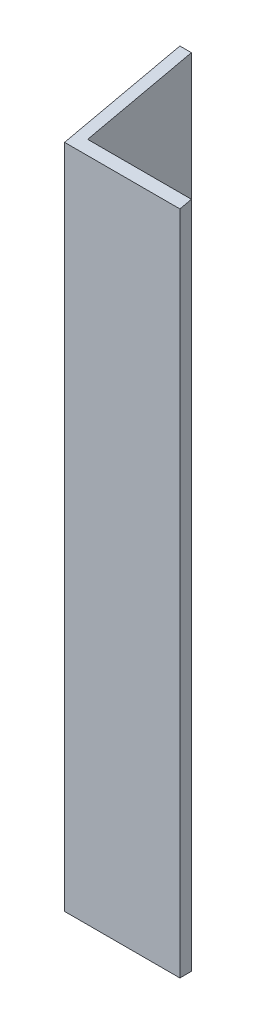
SolidWorks part; units mm, degrees
material "AISI 1020"
ref_plane "Front Plane" through (0, 0, 0) normal (0, 0, 1) x (1, 0, 0)
ref_plane "Top Plane" through (0, 0, 0) normal (0, 1, 0) x (1, 0, 0)
ref_plane "Right Plane" through (0, 0, 0) normal (1, 0, 0) x (0, 0, -1)
sketch "Sketch1" plane through (0, 0, 0) normal (0, 0, 1) x (1, 0, 0)
  line L1 (-3.2273, 4.2045) -> (16.7727, 4.2045)
  line L2 (-3.2273, 4.2045) -> (-3.2273, -115.7955)
  line L3 (-3.2273, -115.7955) -> (16.7727, -115.7955)
  line L4 (16.7727, 4.2045) -> (16.7727, -115.7955)
  dimension "D1" = 20
  dimension "D2" = 120
extrude "Boss-Extrude1" add sketch "Sketch1" against normal blind 20
sketch "Sketch4" plane through (-3.2273, 0, 0) normal (-1, 0, 0) x (0, 0, 1)
  line L0 (-20, 4.2045) -> (0, -0.266)
  line L1 (0, 4.2045) -> (0, -115.7955) construction
  line L2 (0, -0.266) -> (0, 4.2045)
  line L3 (0, 4.2045) -> (-20, 4.2045)
extrude "Cut-Extrude2" cut sketch "Sketch4" against normal blind 20
sketch "Sketch5" plane through (0, -115.7955, 0) normal (0, -1, 0) x (1, 0, 0)
  line L0 (-3.2273, -20) -> (-1.2273, -20)
  line L2 (-3.2273, -20) -> (16.7727, -20) construction
  line L5 (-1.2273, -20) -> (-1.2273, -2)
  line L11 (-1.2273, -2) -> (16.7727, -2)
  line L13 (-1.2273, -20) -> (16.7727, -20)
  line L14 (16.7727, -2) -> (16.7727, -20)
  line M5 (-3.2273, -20) -> (16.7727, -20)
  line M6 (16.7727, -20) -> (16.7727, 0)
  dimension "D1" = 2
  dimension "D2" = 18
extrude "Cut-Extrude4" cut sketch "Sketch5" against normal blind 120 contours L11 L5 M5 M6
